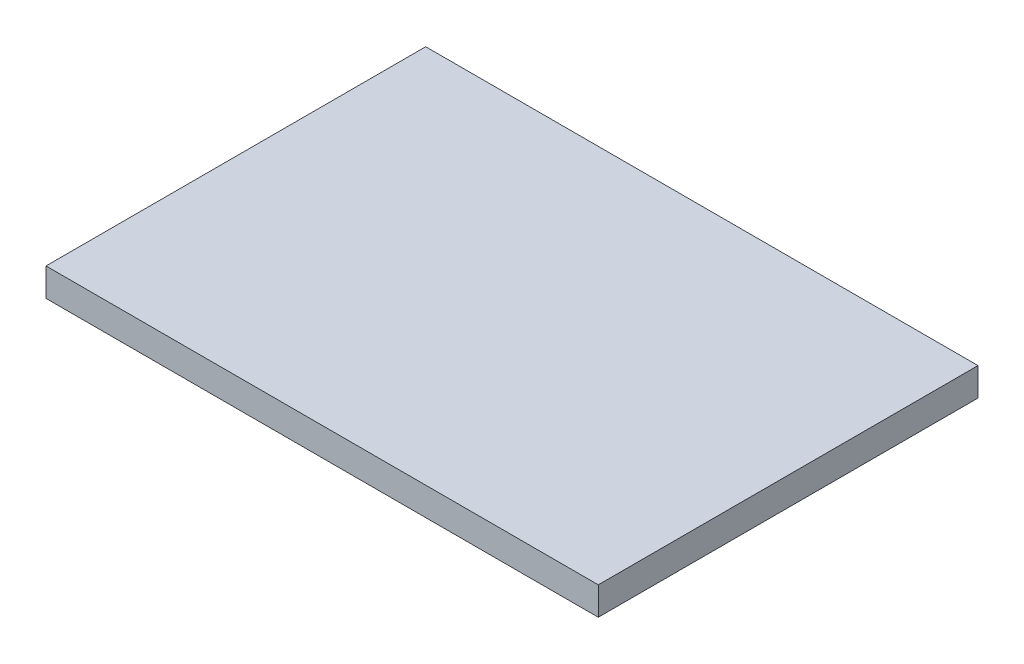
SolidWorks part; units mm, degrees
ref_plane "Front Plane" through (0, 0, 0) normal (0, 0, 1) x (1, 0, 0)
ref_plane "Top Plane" through (0, 0, 0) normal (0, 1, 0) x (1, 0, 0)
ref_plane "Right Plane" through (0, 0, 0) normal (1, 0, 0) x (0, 0, -1)
sketch "Sketch1" plane through (0, 0, 0) normal (0, 1, 0) x (1, 0, 0)
  line L0 (-21.4828, 27) -> (17.7871, 27)
  line L1 (17.7871, 27) -> (17.7871, 0)
  line L2 (17.7871, 0) -> (-21.4828, 0)
  line L3 (-21.4828, 0) -> (-21.4828, 27)
  dimension "D1" = 39.2699
  dimension "D2" = 27
extrude "Boss-Extrude1" add sketch "Sketch1" along normal blind 2
